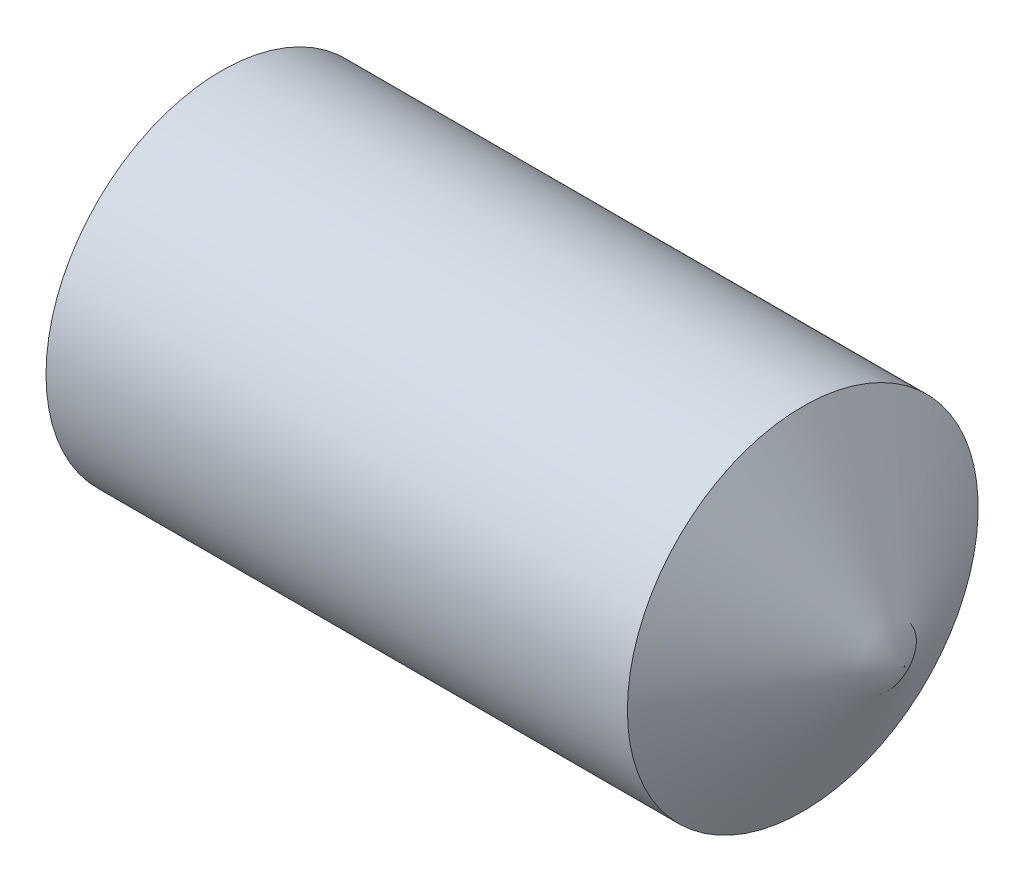
SolidWorks part; units mm, degrees
revolve "BaseBody" add sketch "BodySke" angle 360 about L5
sketch "BodySke" plane through (0, 0, 0) normal (0, 0, 1) x (1, 0, 0)
  line L0 (0, 0) -> (0, 1.2195)
  line L1 (0, 1.2195) -> (0.1619, 1.5)
  line L2 (0.1619, 1.5) -> (5.134, 1.5)
  line L3 (5.134, 1.5) -> (6, 0)
  line L4 (6, 0) -> (0, 0)
  line L5 (-12.7, 0) -> (88.9, 0) construction
  line L6 (5.134, -1.5) -> (6, 0) construction
  line L7 (0.25, 15.875) -> (0.25, -3.175) construction
  line L8 (0, -1.2195) -> (0.1619, -1.5) construction
  dimension "Diameter" = 3
  dimension "Drive_ch_ang" = 60
  dimension "Minor_dia" = 2.439
  dimension "Advance" = 0.5
  dimension "Cone_ang" = 120
  dimension "Length" = 6
cosmetic thread "ThreadCosmetic" [suppressed] parameters "Thread_minor"=2.439
ref_plane "Plane1" through (0, 0, 0) normal (0, 0, 1) x (1, 0, 0)
ref_plane "Plane2" through (0, 0, 0) normal (0, 1, 0) x (1, 0, 0)
ref_plane "Plane3" through (0, 0, 0) normal (1, 0, 0) x (0, 0, -1)
sketch "Sketch2" plane through (0, 0, 0) normal (-1, 0, 0) x (0, 0, 1)
  line L0 (0.433, 0.75) -> (-0.433, 0.75)
  line L1 (-0.433, 0.75) -> (-0.866, 0)
  line L2 (0.433, 0.75) -> (0.866, 0)
  line L3 (0.433, -0.75) -> (0.866, 0)
  line L4 (0.433, -0.75) -> (-0.433, -0.75)
  line L5 (-0.433, -0.75) -> (-0.866, 0)
  dimension "Hex_size" = 1.5
  dimension "D2" = 0.75
  dimension "D3" = 0.75
extrude "Hex" cut sketch "Sketch2" against normal blind 1.2
sketch "ThdSchSke" plane through (0, 0, 0) normal (0, 0, 1) x (1, 0, 0)
  line L0 (0.1619, -1.2195) -> (-0.0345, -1.5)
  line L1 (0.1619, -1.2195) -> (0.3584, -1.5)
  line L2 (0.3584, -1.5) -> (0.3584, -1.875)
  line L3 (-3.175, 0) -> (5.1513, 0) construction
  line L4 (0.1619, 1.5) -> (0.1619, -1.5) construction
  line L5 (0.3584, -1.875) -> (-0.0345, -1.875)
  line L6 (-0.0345, -1.875) -> (-0.0345, -1.5)
  dimension "Thread_minor" = 2.439
  dimension "Diameter" = 3
revolve "ThreadSchematic" [suppressed] cut sketch "ThdSchSke" angle 360 about L3
pattern_linear "ThdSchPat" [suppressed]
equation "\"D2@Sketch2\" = \"Hex_size@Sketch2\" / 2"
equation "\"D3@Sketch2\" = \"Hex_size@Sketch2\" / 2"
equation "\"Thread_minor@ThreadCosmetic\" = \"Minor_dia@BodySke\""
equation "\"Thread_minor@ThdSchSke\" = \"Thread_minor@ThreadCosmetic\""
equation "\"Diameter@ThdSchSke\" = \"Diameter@BodySke\""
equation "\"Overcut@ThdSchSke\" = \"Diameter@BodySke\" * 1.25"
equation "\"Num_threads@ThdSchPat\" = int( (\"Length@BodySke\" - ( ( ( \"Diameter@BodySke\" - \"Minor_dia@BodySke\" ) * 0.5 ) / tan( \"Drive_ch_ang@BodySke\" * 0.017453292 ) ) - ( ( \"Diameter@BodySke\" * 0.5 ) / tan( \"Cone_ang@BodySke\" * 0.008726646 ) ) ) / \"Advance@BodySke\" + 0.999 )  + 1"
equation "\"Advance@ThdSchPat\" = (\"Length@BodySke\" - ( ( ( \"Diameter@BodySke\" - \"Minor_dia@BodySke\" ) * 0.5 ) / tan( \"Drive_ch_ang@BodySke\" * 0.017453292 ) ) - ( ( \"Diameter@BodySke\" * 0.5 ) / tan( \"Cone_ang@BodySke\" * 0.008726646 ) ) ) /  (\"Num_threads@ThdSchPat\" - 1) 'relax it"
equation "' \"Num_threads@ThdSchPat\" = \"Num_threads@ThdSchPat\" - sgn( \"Num_threads@ThdSchPat\" - 1) '---chamfered tips only---"
